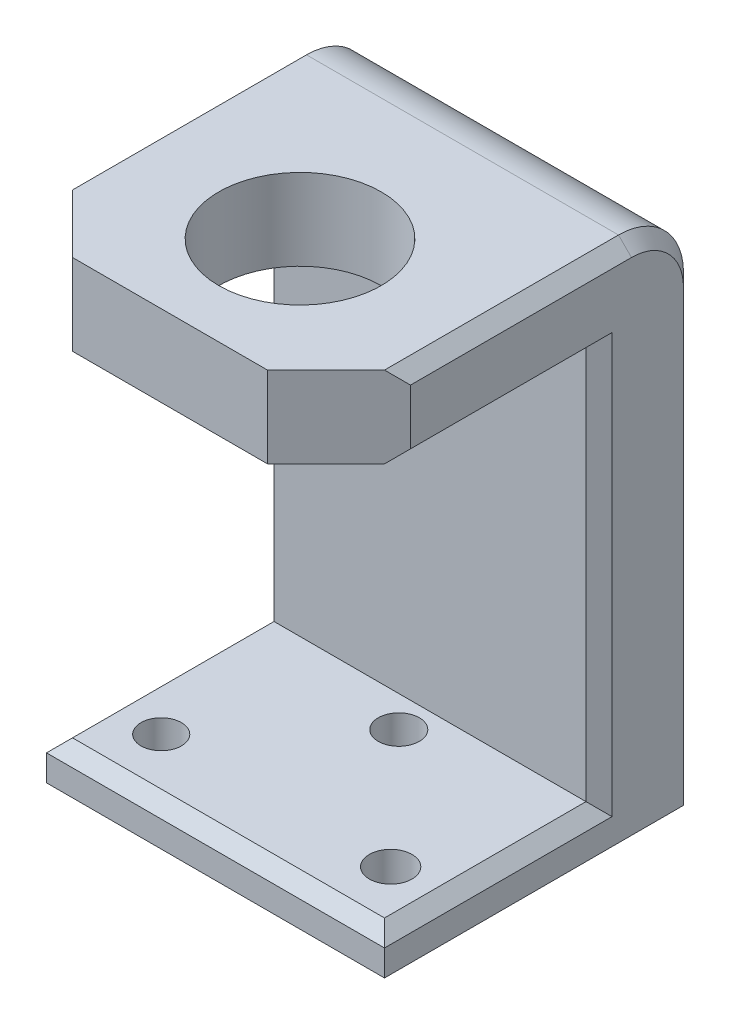
SolidWorks part; units mm, degrees
ref_plane "Front Plane" through (0, 0, 0) normal (0, 0, 1) x (1, 0, 0)
ref_plane "Top Plane" through (0, 0, 0) normal (0, 1, 0) x (1, 0, 0)
ref_plane "Right Plane" through (0, 0, 0) normal (1, 0, 0) x (0, 0, -1)
sketch "Sketch1" plane through (0, 0, 0) normal (0, 1, 0) x (1, 0, 0)
  line L15 (-43.4955, -30.5508) -> (-43.4955, -91.5108)
  line L22 (11.94, -79.7003) -> (-32.891, -79.7003) construction
  line L35 (-43.4955, -30.5508) -> (22.5445, -30.5508)
  line L36 (-43.4955, -91.5108) -> (22.5445, -91.5108)
  line L37 (22.5445, -30.5508) -> (22.5445, -91.5108)
  circle A3 centre (-32.891, -79.7003) radius 3.9496
  circle A4 centre (11.94, -79.7003) radius 4.1699
  circle A5 centre (-10.4755, -55.6973) radius 4.0094
  point P0 (0, 0)
  point P1 (-10.4755, -30.5508)
  point P3 (0, 0)
  point P5 (0, 0)
  point P7 (-10.4755, -79.7003)
  dimension "D3" = 44.831
  dimension "D4" = 24.003
  dimension "D5" = 24.003
  dimension "D6" = 60.96
  dimension "D7" = 66.04
extrude "Boss-Extrude1" add sketch "Sketch1" along normal blind 7.62
sketch "Sketch3" plane through (0, 7.62, 0) normal (0, 1, 0) x (1, 0, 0)
  line L1 (-43.4955, -49.6008) -> (22.5445, -49.6008)
  line L2 (-43.4955, -49.6008) -> (-43.4955, -30.5508)
  line L3 (-43.4955, -30.5508) -> (22.5445, -30.5508)
  line L4 (22.5445, -49.6008) -> (22.5445, -30.5508)
  line L5 (22.5445, -30.5508) -> (-43.4955, -30.5508) construction
  point P6 (-10.4755, -30.5508)
  point P7 (-10.4755, -30.5508)
  dimension "D1" = 19.05
  dimension "D2" = 66.04
extrude "Boss-Extrude2" add sketch "Sketch3" along normal blind 92.71
sketch "Sketch4" plane through (0, 0, 49.6008) normal (0, 0, 1) x (1, 0, 0)
  line L1 (-43.4955, 100.33) -> (22.5445, 100.33)
  line L2 (-43.4955, 100.33) -> (-43.4955, 84.455)
  line L3 (-43.4955, 84.455) -> (22.5445, 84.455)
  line L4 (22.5445, 100.33) -> (22.5445, 84.455)
  line L5 (-43.4955, 100.33) -> (22.5445, 100.33) construction
  point P4 (-10.4755, 100.33)
  point P7 (-10.4755, 100.33)
  dimension "D1" = 15.875
  dimension "D2" = 66.04
extrude "Boss-Extrude3" add sketch "Sketch4" along normal blind 50.8
sketch "Sketch5" plane through (0, 100.33, 0) normal (0, 1, 0) x (1, 0, 0)
  line L0 (22.5445, -100.4008) -> (-43.4955, -100.4008) construction
  circle A0 centre (-10.4755, -75.0008) radius 15.875
  point P5 (-10.4755, -100.4008)
  dimension "D1" = 31.75
  dimension "D2" = 25.4
extrude "Cut-Extrude2" cut sketch "Sketch5" against normal blind 15.875
fillet "Fillet1" radius 12.7 1 edges at (-10.4755, 100.33, 30.5508)
chamfer "Chamfer2" distance 2.54 angle 45 13 edges at (22.5445, 84.455, 75.0008) (22.5445, 100.33, 71.8258) (22.5445, 43.815, 30.5508) (-43.4955, 84.455, 75.0008) (-43.4955, 100.33, 71.8258) (-43.4955, 43.815, 30.5508) (22.5445, 96.6103, 34.2705) (22.5445, 7.62, 70.5558) (22.5445, 46.0375, 49.6008) (-43.4955, 7.62, 70.5558) (-43.4955, 46.0375, 49.6008) (-43.4955, 96.6103, 34.2705) (-10.4755, 7.62, 91.5108)
chamfer "Chamfer3" distance 13.97 angle 45 2 edges at (-43.4955, 92.3925, 100.4008) (22.5445, 92.3925, 100.4008)
